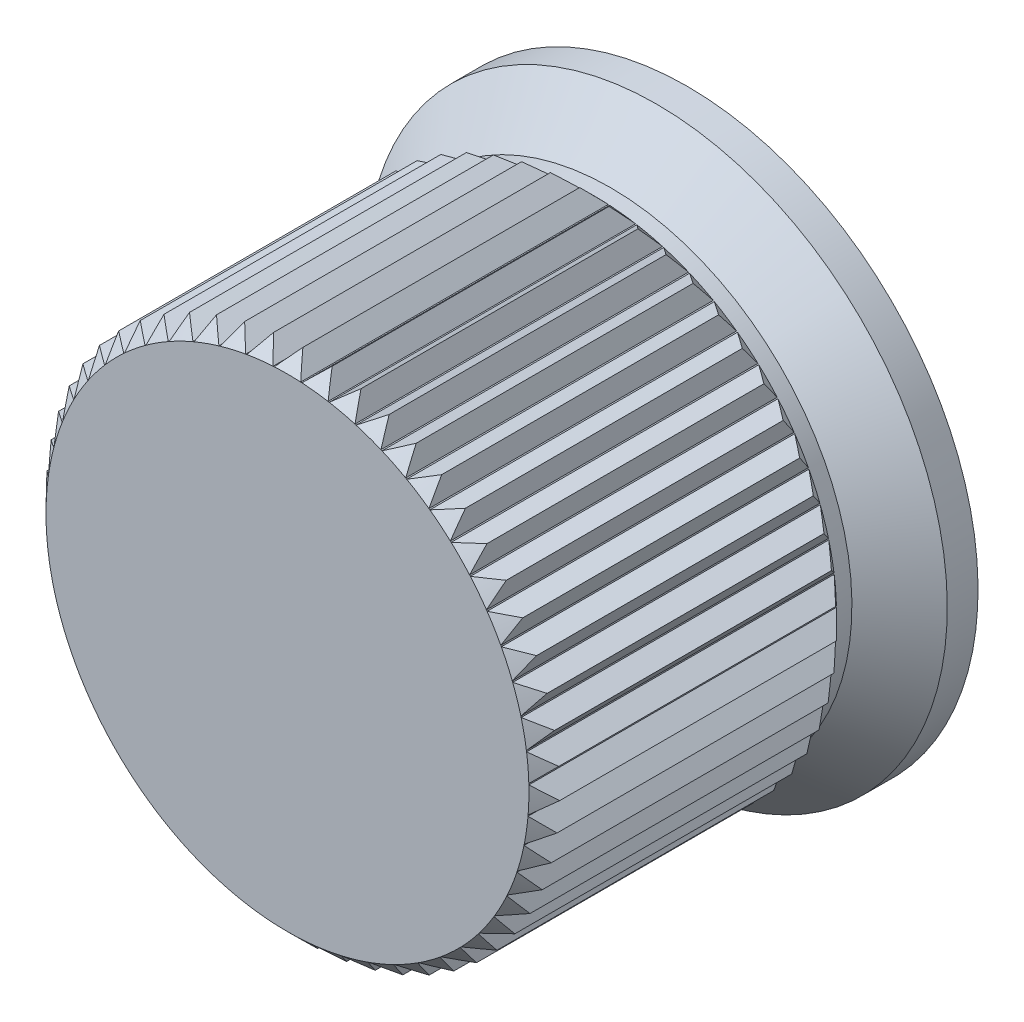
SolidWorks part; units mm, degrees
material "Plain Carbon Steel"
ref_plane "Front Plane" through (0, 0, 0) normal (0, 0, 1) x (1, 0, 0)
ref_plane "Top Plane" through (0, 0, 0) normal (0, 1, 0) x (1, 0, 0)
ref_plane "Right Plane" through (0, 0, 0) normal (1, 0, 0) x (0, 0, -1)
sketch "Sketch1" plane through (0, 0, 0) normal (1, 0, 0) x (0, 0, -1)
  line L0 (0, 0) -> (-10.5, 0) construction
  line L1 (-10.5, 0) -> (-10.5, 7.85)
  line L2 (-10.5, 7.85) -> (0, 7.85)
  line L3 (0, 7.85) -> (1.5, 9.45)
  line L4 (1.5, 9.45) -> (2.5, 9.45)
  line L5 (2.5, 9.45) -> (2.5, 7)
  line L6 (2.5, 7) -> (0, 7)
  line L7 (0, 7) -> (0, 0)
  line L8 (0, 0) -> (-10.5, 0)
  dimension "D1" = 13
  dimension "D2" = 9.45
  dimension "D3" = 7
  dimension "D4" = 1
  dimension "D5" = 2.5
  dimension "D6" = 10.5
  dimension "D7" = 7.85
revolve "Revolve1" add sketch "Sketch1" angle 360 about L0
sketch "Sketch2" plane through (0, 0, 10.5) normal (0, 0, 1) x (1, 0, 0)
  line L0 (0, 0) -> (0, 7.85) construction
  line L1 (0, 7.85) -> (0, 8.35) construction
  line L2 (0, 8.35) -> (0.4294, 7.8382)
  line L3 (0, 8.35) -> (-0.4294, 7.8382)
  line L4 (-0.4294, 7.8382) -> (0.4294, 7.8382)
  circle A0 centre (0, 0) radius 7.85 construction
  circle A1 centre (0, 0) radius 7.85 construction
  dimension "D1" = 0.5
  dimension "D2" = 80
extrude "Boss-Extrude1" add sketch "Sketch2" against normal blind 10
pattern_circular "CirPattern1" count 55 over 360 about axis through (0, 0, 0) along (0, 0, 1) of "Boss-Extrude1"
sketch "Sketch3" plane through (0, 0, 0) normal (1, 0, 0) x (0, 0, -1)
  line L0 (0, 0) -> (-11.9402, 0) construction
  line L2 (-10.5, 7.85) -> (-10, 8.35)
  line L3 (-10, 8.35) -> (-10.5, 8.35)
  line L4 (-10.5, 8.35) -> (-10.5, 7.85)
  line L5 (-1, 8.35) -> (-0.5, 8.35)
  line L6 (-0.5, 8.35) -> (-0.5, 7.85)
  line L7 (-0.5, 7.85) -> (-1, 8.35)
  dimension "D1" = 0.5
revolve "Cut-Revolve1" cut sketch "Sketch3" angle 360 about L0
sketch "Sketch4" plane through (0, 0, 0) normal (0, 0, -1) x (-1, 0, 0)
  circle A0 centre (0, 0) radius 3
  dimension "D1" = 6
extrude "Cut-Extrude1" cut sketch "Sketch4" against normal blind 8
